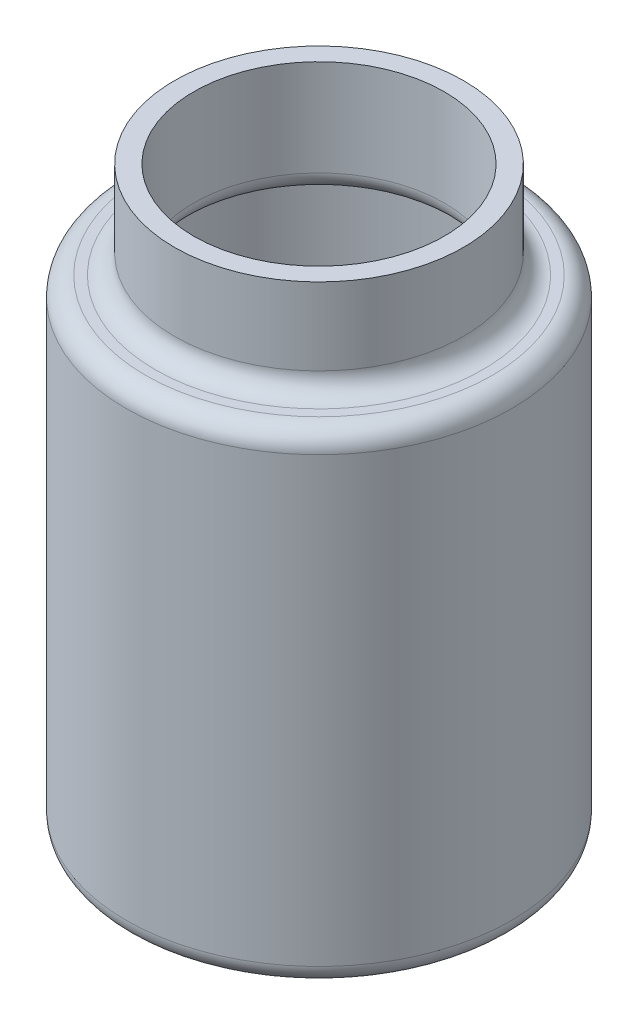
SolidWorks part; units mm, degrees
material "PET"
ref_plane "Front Plane" through (0, 0, 0) normal (0, 0, 1) x (1, 0, 0)
ref_plane "Top Plane" through (0, 0, 0) normal (0, 1, 0) x (1, 0, 0)
ref_plane "Right Plane" through (0, 0, 0) normal (1, 0, 0) x (0, 0, -1)
sketch "Sketch1" plane through (0, 0, 0) normal (0, 0, 1) x (1, 0, 0)
  line L0 (0, 30) -> (0, 44.0747) construction
  line L1 (0, 0) -> (0, 30)
  line L2 (0, 0) -> (-10, 0)
  line L4 (-7.5, 25) -> (-10, 25)
  line L5 (-10, 0) -> (-10, 25)
  line L8 (0, 30) -> (-7.5, 30)
  line L9 (-7.5, 25) -> (-7.5, 30)
  dimension "D1" = 25
  dimension "D2" = 20
  dimension "D3" = 5
  dimension "D4" = 15
revolve "Revolve1" add sketch "Sketch1" angle 360 about L0
shell "Shell1" thickness 1
fillet "Fillet1" radius 1 3 edges at (0, 25, -7.5) (0, 0, -10) (0, 25, -10)
fillet "Fillet2" radius 1 1 edges at (0, 24, -6.5)
